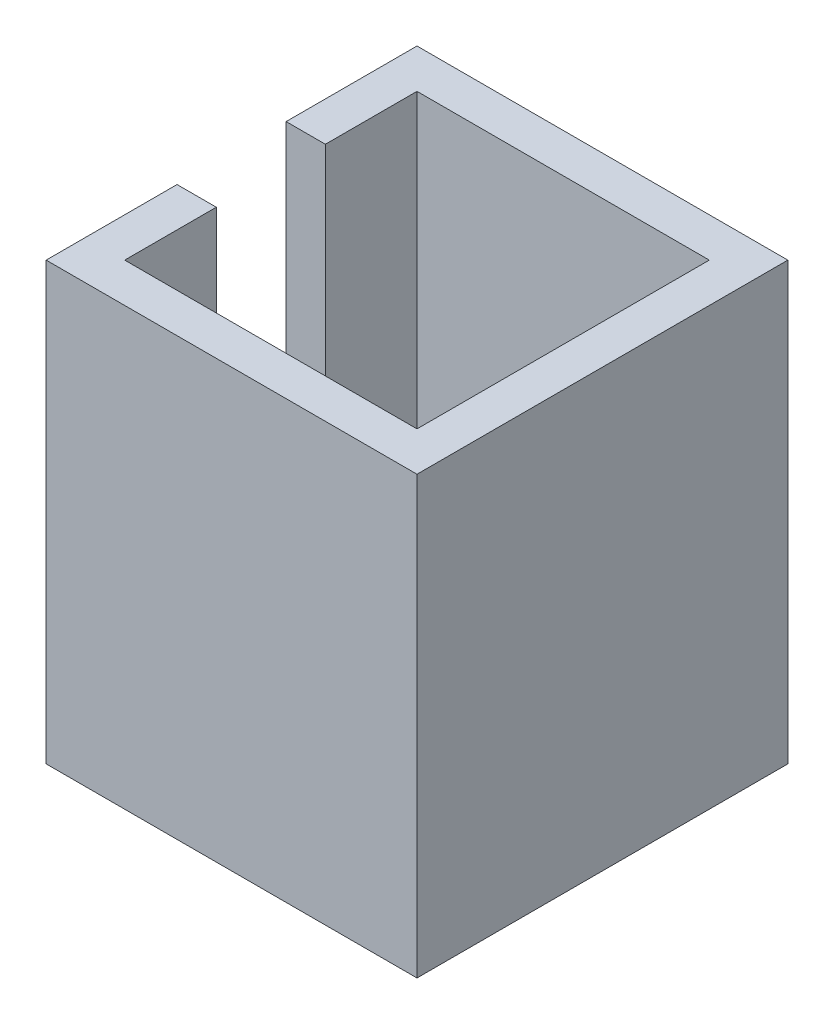
SolidWorks part; units mm, degrees
ref_plane "Front Plane" through (0, 0, 0) normal (0, 0, 1) x (1, 0, 0)
ref_plane "Top Plane" through (0, 0, 0) normal (0, 1, 0) x (1, 0, 0)
ref_plane "Right Plane" through (0, 0, 0) normal (1, 0, 0) x (0, 0, -1)
sketch "Sketch1" plane through (0, 0, 0) normal (0, 1, 0) x (1, 0, 0)
  line L1 (0, 0) -> (17, 0)
  line L2 (0, 0) -> (0, 17)
  line L3 (0, 17) -> (17, 17)
  line L4 (17, 0) -> (17, 17)
  dimension "D1" = 17
  dimension "D2" = 17
extrude "Boss-Extrude1" add sketch "Sketch1" along normal blind 20
shell "Shell1" thickness 1.8
hole_wizard "Ø6.5 (6.5) Diameter Hole1" positions "Sketch3" profile "Sketch4" hole size "Ø6.5" standard "ANSI Metric" end condition through all
sketch "Sketch3" plane through (0, 0, 0) normal (0, -1, 0) x (-1, 0, 0)
  line L0 (0, 0) -> (-17, 0) construction
  line L1 (-17, 0) -> (-17, 17) construction
  point P0 (-8.5, 8.5)
  point P9 (-7.5, 8.5)
  point P10 (0, 0)
  dimension "D1" = 8.5
  dimension "D2" = 8.5
sketch "Sketch4" plane through (8.5, 0, -8.5) normal (1, 0, 0) x (0, 0, -1)
  line L0 (0, 0) -> (0, 20)
  line L1 (0, 20) -> (3.25, 20)
  line L2 (3.25, 20) -> (3.25, 0)
  line L5 (3.25, 0) -> (0, 0)
  line L11 (0, -6.35) -> (0, 107.95) construction
  dimension "Thru Hole Dia." = 6.5
  dimension "Thru Hole Depth" = 20
sketch "Sketch5" plane through (0, 0, 0) normal (-1, 0, 0) x (0, 0, 1)
  line L0 (-17, 20) -> (0, 20) construction
  line L1 (-6, 4.9777) -> (-11, 4.9777)
  line L2 (-6, 4.9777) -> (-6, 20)
  line L3 (-6, 20) -> (-11, 20)
  line L4 (-11, 4.9777) -> (-11, 20)
  line L5 (-6, 4.9777) -> (-11, 20) construction
  line L6 (-6, 20) -> (-11, 4.9777) construction
  line L7 (0, 20) -> (0, 0) construction
  point P0 (-8.5, 12.4889)
  dimension "D1" = 6
  dimension "D2" = 5
extrude "Cut-Extrude1" cut sketch "Sketch5" against normal blind 4
